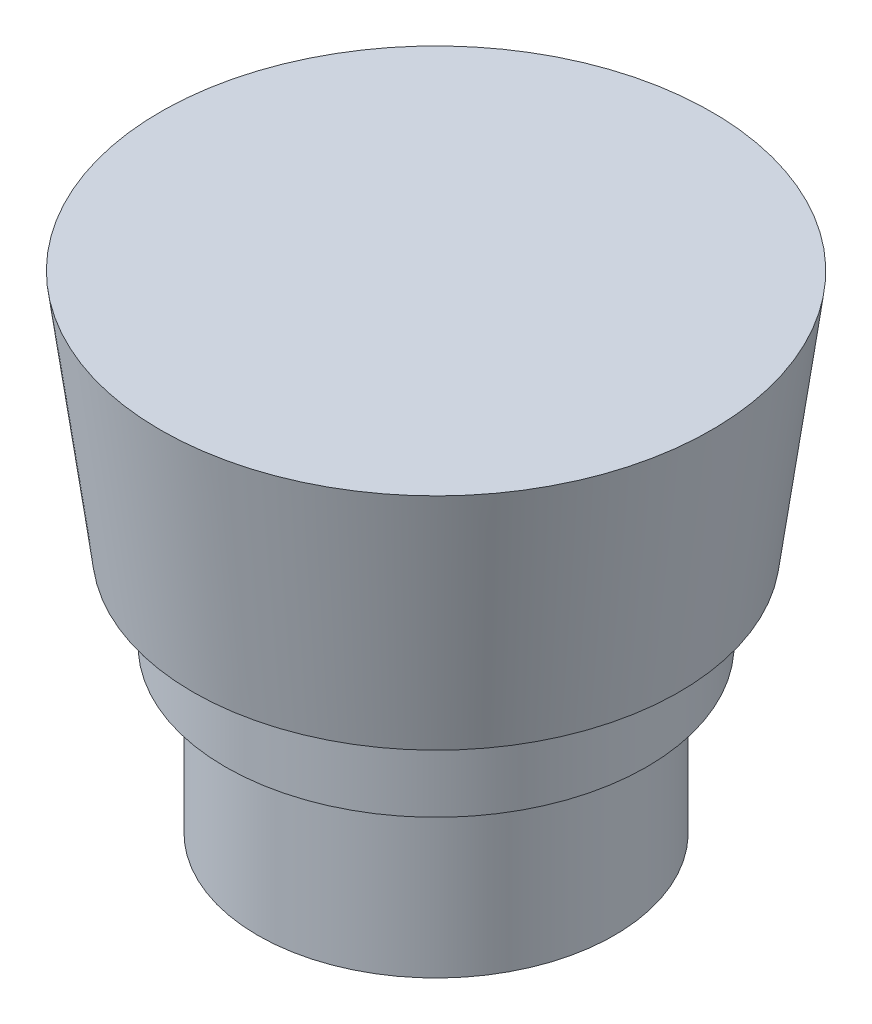
SolidWorks part; units mm, degrees
ref_plane "Plan de face" through (0, 0, 0) normal (0, 0, 1) x (1, 0, 0)
ref_plane "Plan de dessus" through (0, 0, 0) normal (0, 1, 0) x (1, 0, 0)
ref_plane "Plan de droite" through (0, 0, 0) normal (1, 0, 0) x (0, 0, -1)
sketch "Esquisse1" plane through (0, 0, 0) normal (0, 0, 1) x (1, 0, 0)
  line L0 (0, 48.227) -> (0, -47.7784) construction
  line L1 (0, -30.5353) -> (11, -30.5353)
  line L2 (13, -15.5353) -> (13, -20.5353)
  line L3 (13, -15.5353) -> (15, -15.5353)
  line L4 (15, -15.5353) -> (17, -0.5353)
  line L5 (17, -0.5353) -> (0, -0.5353)
  line L6 (0, -0.5353) -> (0, -30.5353)
  line L7 (13, -20.5353) -> (11, -20.5353)
  line L8 (11, -20.5353) -> (11, -30.5353)
  dimension "D1" = 30
  dimension "D2" = 15
  dimension "D3" = 11
  dimension "D4" = 17
  dimension "D5" = 2
  dimension "D6" = 2
  dimension "D7" = 90
  dimension "D8" = 10
revolve "Révolution1" add sketch "Esquisse1" angle 360 about L0
